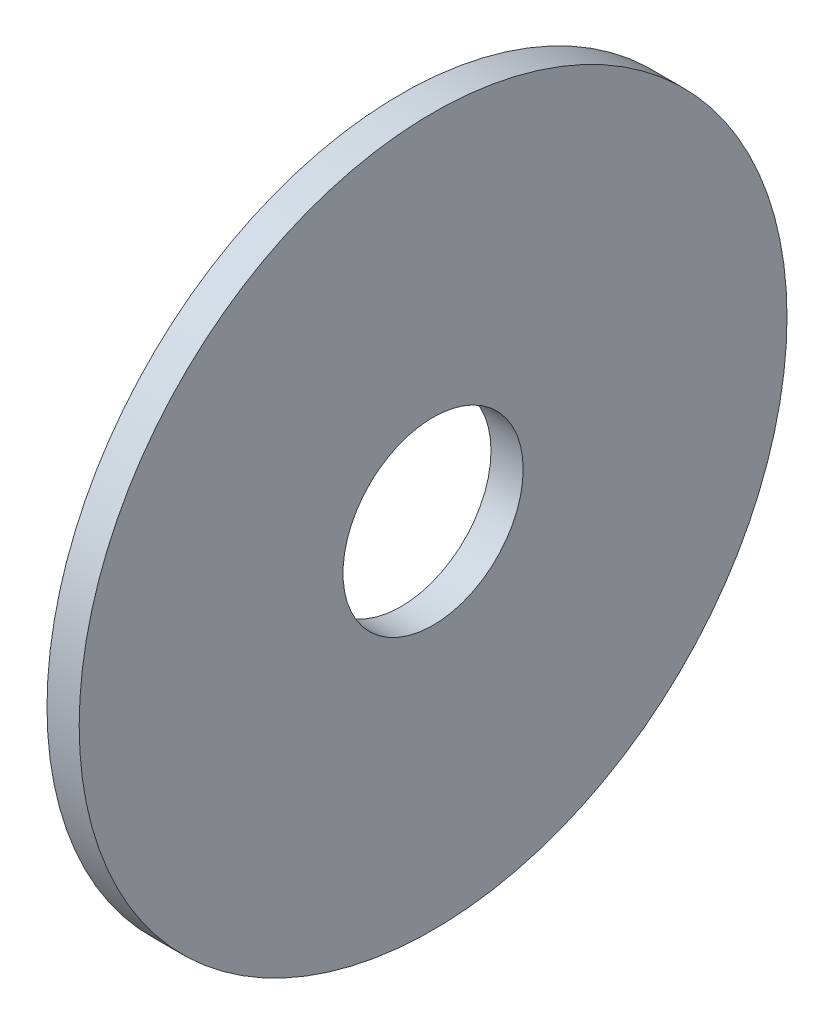
SolidWorks part; units mm, degrees
material "Простая углеродистая сталь"
ref_plane "Front" through (0, 0, 0) normal (0, 0, 1) x (1, 0, 0)
ref_plane "Top" through (0, 0, 0) normal (0, 1, 0) x (1, 0, 0)
ref_plane "Right" through (0, 0, 0) normal (1, 0, 0) x (0, 0, -1)
sketch "Эскиз1" plane through (0, 0, 0) normal (1, 0, 0) x (0, 0, -1)
  circle A0 centre (0, 0) radius 14
  circle A1 centre (0, 0) radius 55
  dimension "D1" = 28
extrude "Бобышка-Вытянуть1" add sketch "Эскиз1" along normal blind 5
